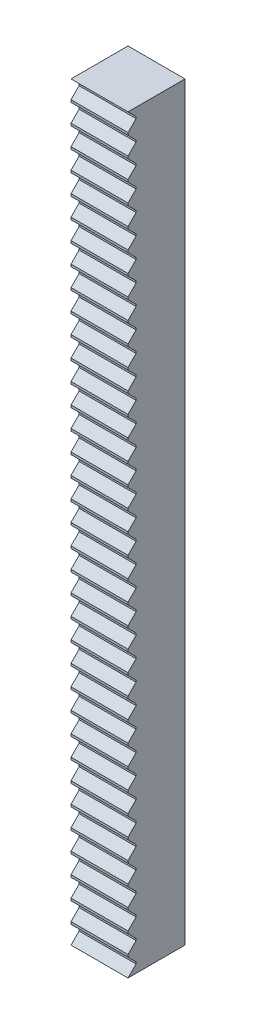
SolidWorks part; units mm, degrees
ref_plane "Front Plane" through (0, 0, 0) normal (0, 0, 1) x (1, 0, 0)
ref_plane "Top Plane" through (0, 0, 0) normal (0, 1, 0) x (1, 0, 0)
ref_plane "Right Plane" through (0, 0, 0) normal (1, 0, 0) x (0, 0, -1)
sketch "Sketch1" plane through (0, 0, 0) normal (0, 0, 1) x (1, 0, 0)
  line L1 (-9.5, 125) -> (9.5, 125)
  line L2 (-9.5, 125) -> (-9.5, -125)
  line L3 (-9.5, -125) -> (9.5, -125)
  line L4 (9.5, 125) -> (9.5, -125)
  line L5 (-9.5, 125) -> (9.5, -125) construction
  line L6 (-9.5, -125) -> (9.5, 125) construction
  point P0 (0, 0)
  dimension "D1" = 19
  dimension "D2" = 250
extrude "Boss-Extrude1" add sketch "Sketch1" along normal mid plane 19
sketch "Sketch2" plane through (-9.5, 0, 0) normal (-1, 0, 0) x (0, 0, 1)
  line L0 (9.5, 125) -> (6.8, 122.3)
  line L1 (6.8, 121.7) -> (9.5, 119)
  line L3 (9.5, 125) -> (9.5, -125) construction
  line L6 (9.5, 125) -> (10.5, 125)
  line L7 (10.5, 125) -> (10.5, 119)
  line L8 (10.5, 119) -> (9.5, 119)
  line L9 (6.8, 122.3) -> (6.8, 121.7)
  line L10 (9.5, 118.2222) -> (6.8, 115.5222)
  line L11 (6.8, 114.9222) -> (9.5, 112.2222)
  line L12 (9.5, 118.2222) -> (10.5, 118.2222)
  line L13 (10.5, 118.2222) -> (10.5, 112.2222)
  line L14 (10.5, 112.2222) -> (9.5, 112.2222)
  line L15 (6.8, 115.5222) -> (6.8, 114.9222)
  line L16 (9.5, 111.4444) -> (6.8, 108.7444)
  line L17 (6.8, 108.1444) -> (9.5, 105.4444)
  line L18 (9.5, 111.4444) -> (10.5, 111.4444)
  line L19 (10.5, 111.4444) -> (10.5, 105.4444)
  line L20 (10.5, 105.4444) -> (9.5, 105.4444)
  line L21 (6.8, 108.7444) -> (6.8, 108.1444)
  line L22 (9.5, 104.6667) -> (6.8, 101.9667)
  line L23 (6.8, 101.3667) -> (9.5, 98.6667)
  line L24 (9.5, 104.6667) -> (10.5, 104.6667)
  line L25 (10.5, 104.6667) -> (10.5, 98.6667)
  line L26 (10.5, 98.6667) -> (9.5, 98.6667)
  line L27 (6.8, 101.9667) -> (6.8, 101.3667)
  line L28 (9.5, 97.8889) -> (6.8, 95.1889)
  line L29 (6.8, 94.5889) -> (9.5, 91.8889)
  line L30 (9.5, 97.8889) -> (10.5, 97.8889)
  line L31 (10.5, 97.8889) -> (10.5, 91.8889)
  line L32 (10.5, 91.8889) -> (9.5, 91.8889)
  line L33 (6.8, 95.1889) -> (6.8, 94.5889)
  line L34 (9.5, 91.1111) -> (6.8, 88.4111)
  line L35 (6.8, 87.8111) -> (9.5, 85.1111)
  line L36 (9.5, 91.1111) -> (10.5, 91.1111)
  line L37 (10.5, 91.1111) -> (10.5, 85.1111)
  line L38 (10.5, 85.1111) -> (9.5, 85.1111)
  line L39 (6.8, 88.4111) -> (6.8, 87.8111)
  line L40 (9.5, 84.3333) -> (6.8, 81.6333)
  line L41 (6.8, 81.0333) -> (9.5, 78.3333)
  line L42 (9.5, 84.3333) -> (10.5, 84.3333)
  line L43 (10.5, 84.3333) -> (10.5, 78.3333)
  line L44 (10.5, 78.3333) -> (9.5, 78.3333)
  line L45 (6.8, 81.6333) -> (6.8, 81.0333)
  line L46 (9.5, 77.5556) -> (6.8, 74.8556)
  line L47 (6.8, 74.2556) -> (9.5, 71.5556)
  line L48 (9.5, 77.5556) -> (10.5, 77.5556)
  line L49 (10.5, 77.5556) -> (10.5, 71.5556)
  line L50 (10.5, 71.5556) -> (9.5, 71.5556)
  line L51 (6.8, 74.8556) -> (6.8, 74.2556)
  line L52 (9.5, 70.7778) -> (6.8, 68.0778)
  line L53 (6.8, 67.4778) -> (9.5, 64.7778)
  line L54 (9.5, 70.7778) -> (10.5, 70.7778)
  line L55 (10.5, 70.7778) -> (10.5, 64.7778)
  line L56 (10.5, 64.7778) -> (9.5, 64.7778)
  line L57 (6.8, 68.0778) -> (6.8, 67.4778)
  line L58 (9.5, 64) -> (6.8, 61.3)
  line L59 (6.8, 60.7) -> (9.5, 58)
  line L60 (9.5, 64) -> (10.5, 64)
  line L61 (10.5, 64) -> (10.5, 58)
  line L62 (10.5, 58) -> (9.5, 58)
  line L63 (6.8, 61.3) -> (6.8, 60.7)
  line L64 (9.5, 57.2222) -> (6.8, 54.5222)
  line L65 (6.8, 53.9222) -> (9.5, 51.2222)
  line L66 (9.5, 57.2222) -> (10.5, 57.2222)
  line L67 (10.5, 57.2222) -> (10.5, 51.2222)
  line L68 (10.5, 51.2222) -> (9.5, 51.2222)
  line L69 (6.8, 54.5222) -> (6.8, 53.9222)
  line L70 (9.5, 50.4444) -> (6.8, 47.7444)
  line L71 (6.8, 47.1444) -> (9.5, 44.4444)
  line L72 (9.5, 50.4444) -> (10.5, 50.4444)
  line L73 (10.5, 50.4444) -> (10.5, 44.4444)
  line L74 (10.5, 44.4444) -> (9.5, 44.4444)
  line L75 (6.8, 47.7444) -> (6.8, 47.1444)
  line L76 (9.5, 43.6667) -> (6.8, 40.9667)
  line L77 (6.8, 40.3667) -> (9.5, 37.6667)
  line L78 (9.5, 43.6667) -> (10.5, 43.6667)
  line L79 (10.5, 43.6667) -> (10.5, 37.6667)
  line L80 (10.5, 37.6667) -> (9.5, 37.6667)
  line L81 (6.8, 40.9667) -> (6.8, 40.3667)
  line L82 (9.5, 36.8889) -> (6.8, 34.1889)
  line L83 (6.8, 33.5889) -> (9.5, 30.8889)
  line L84 (9.5, 36.8889) -> (10.5, 36.8889)
  line L85 (10.5, 36.8889) -> (10.5, 30.8889)
  line L86 (10.5, 30.8889) -> (9.5, 30.8889)
  line L87 (6.8, 34.1889) -> (6.8, 33.5889)
  line L88 (9.5, 30.1111) -> (6.8, 27.4111)
  line L89 (6.8, 26.8111) -> (9.5, 24.1111)
  line L90 (9.5, 30.1111) -> (10.5, 30.1111)
  line L91 (10.5, 30.1111) -> (10.5, 24.1111)
  line L92 (10.5, 24.1111) -> (9.5, 24.1111)
  line L93 (6.8, 27.4111) -> (6.8, 26.8111)
  line L94 (9.5, 23.3333) -> (6.8, 20.6333)
  line L95 (6.8, 20.0333) -> (9.5, 17.3333)
  line L96 (9.5, 23.3333) -> (10.5, 23.3333)
  line L97 (10.5, 23.3333) -> (10.5, 17.3333)
  line L98 (10.5, 17.3333) -> (9.5, 17.3333)
  line L99 (6.8, 20.6333) -> (6.8, 20.0333)
  line L100 (9.5, 16.5556) -> (6.8, 13.8556)
  line L101 (6.8, 13.2556) -> (9.5, 10.5556)
  line L102 (9.5, 16.5556) -> (10.5, 16.5556)
  line L103 (10.5, 16.5556) -> (10.5, 10.5556)
  line L104 (10.5, 10.5556) -> (9.5, 10.5556)
  line L105 (6.8, 13.8556) -> (6.8, 13.2556)
  line L106 (9.5, 9.7778) -> (6.8, 7.0778)
  line L107 (6.8, 6.4778) -> (9.5, 3.7778)
  line L108 (9.5, 9.7778) -> (10.5, 9.7778)
  line L109 (10.5, 9.7778) -> (10.5, 3.7778)
  line L110 (10.5, 3.7778) -> (9.5, 3.7778)
  line L111 (6.8, 7.0778) -> (6.8, 6.4778)
  line L112 (9.5, 3) -> (6.8, 0.3)
  line L113 (6.8, -0.3) -> (9.5, -3)
  line L114 (9.5, 3) -> (10.5, 3)
  line L115 (10.5, 3) -> (10.5, -3)
  line L116 (10.5, -3) -> (9.5, -3)
  line L117 (6.8, 0.3) -> (6.8, -0.3)
  line L118 (9.5, -3.7778) -> (6.8, -6.4778)
  line L119 (6.8, -7.0778) -> (9.5, -9.7778)
  line L120 (9.5, -3.7778) -> (10.5, -3.7778)
  line L121 (10.5, -3.7778) -> (10.5, -9.7778)
  line L122 (10.5, -9.7778) -> (9.5, -9.7778)
  line L123 (6.8, -6.4778) -> (6.8, -7.0778)
  line L124 (9.5, -10.5556) -> (6.8, -13.2556)
  line L125 (6.8, -13.8556) -> (9.5, -16.5556)
  line L126 (9.5, -10.5556) -> (10.5, -10.5556)
  line L127 (10.5, -10.5556) -> (10.5, -16.5556)
  line L128 (10.5, -16.5556) -> (9.5, -16.5556)
  line L129 (6.8, -13.2556) -> (6.8, -13.8556)
  line L130 (9.5, -17.3333) -> (6.8, -20.0333)
  line L131 (6.8, -20.6333) -> (9.5, -23.3333)
  line L132 (9.5, -17.3333) -> (10.5, -17.3333)
  line L133 (10.5, -17.3333) -> (10.5, -23.3333)
  line L134 (10.5, -23.3333) -> (9.5, -23.3333)
  line L135 (6.8, -20.0333) -> (6.8, -20.6333)
  line L136 (9.5, -24.1111) -> (6.8, -26.8111)
  line L137 (6.8, -27.4111) -> (9.5, -30.1111)
  line L138 (9.5, -24.1111) -> (10.5, -24.1111)
  line L139 (10.5, -24.1111) -> (10.5, -30.1111)
  line L140 (10.5, -30.1111) -> (9.5, -30.1111)
  line L141 (6.8, -26.8111) -> (6.8, -27.4111)
  line L142 (9.5, -30.8889) -> (6.8, -33.5889)
  line L143 (6.8, -34.1889) -> (9.5, -36.8889)
  line L144 (9.5, -30.8889) -> (10.5, -30.8889)
  line L145 (10.5, -30.8889) -> (10.5, -36.8889)
  line L146 (10.5, -36.8889) -> (9.5, -36.8889)
  line L147 (6.8, -33.5889) -> (6.8, -34.1889)
  line L148 (9.5, -37.6667) -> (6.8, -40.3667)
  line L149 (6.8, -40.9667) -> (9.5, -43.6667)
  line L150 (9.5, -37.6667) -> (10.5, -37.6667)
  line L151 (10.5, -37.6667) -> (10.5, -43.6667)
  line L152 (10.5, -43.6667) -> (9.5, -43.6667)
  line L153 (6.8, -40.3667) -> (6.8, -40.9667)
  line L154 (9.5, -44.4444) -> (6.8, -47.1444)
  line L155 (6.8, -47.7444) -> (9.5, -50.4444)
  line L156 (9.5, -44.4444) -> (10.5, -44.4444)
  line L157 (10.5, -44.4444) -> (10.5, -50.4444)
  line L158 (10.5, -50.4444) -> (9.5, -50.4444)
  line L159 (6.8, -47.1444) -> (6.8, -47.7444)
  line L160 (9.5, -51.2222) -> (6.8, -53.9222)
  line L161 (6.8, -54.5222) -> (9.5, -57.2222)
  line L162 (9.5, -51.2222) -> (10.5, -51.2222)
  line L163 (10.5, -51.2222) -> (10.5, -57.2222)
  line L164 (10.5, -57.2222) -> (9.5, -57.2222)
  line L165 (6.8, -53.9222) -> (6.8, -54.5222)
  line L166 (9.5, -58) -> (6.8, -60.7)
  line L167 (6.8, -61.3) -> (9.5, -64)
  line L168 (9.5, -58) -> (10.5, -58)
  line L169 (10.5, -58) -> (10.5, -64)
  line L170 (10.5, -64) -> (9.5, -64)
  line L171 (6.8, -60.7) -> (6.8, -61.3)
  line L172 (9.5, -64.7778) -> (6.8, -67.4778)
  line L173 (6.8, -68.0778) -> (9.5, -70.7778)
  line L174 (9.5, -64.7778) -> (10.5, -64.7778)
  line L175 (10.5, -64.7778) -> (10.5, -70.7778)
  line L176 (10.5, -70.7778) -> (9.5, -70.7778)
  line L177 (6.8, -67.4778) -> (6.8, -68.0778)
  line L178 (9.5, -71.5556) -> (6.8, -74.2556)
  line L179 (6.8, -74.8556) -> (9.5, -77.5556)
  line L180 (9.5, -71.5556) -> (10.5, -71.5556)
  line L181 (10.5, -71.5556) -> (10.5, -77.5556)
  line L182 (10.5, -77.5556) -> (9.5, -77.5556)
  line L183 (6.8, -74.2556) -> (6.8, -74.8556)
  line L184 (9.5, -78.3333) -> (6.8, -81.0333)
  line L185 (6.8, -81.6333) -> (9.5, -84.3333)
  line L186 (9.5, -78.3333) -> (10.5, -78.3333)
  line L187 (10.5, -78.3333) -> (10.5, -84.3333)
  line L188 (10.5, -84.3333) -> (9.5, -84.3333)
  line L189 (6.8, -81.0333) -> (6.8, -81.6333)
  line L190 (9.5, -85.1111) -> (6.8, -87.8111)
  line L191 (6.8, -88.4111) -> (9.5, -91.1111)
  line L192 (9.5, -85.1111) -> (10.5, -85.1111)
  line L193 (10.5, -85.1111) -> (10.5, -91.1111)
  line L194 (10.5, -91.1111) -> (9.5, -91.1111)
  line L195 (6.8, -87.8111) -> (6.8, -88.4111)
  line L196 (9.5, -91.8889) -> (6.8, -94.5889)
  line L197 (6.8, -95.1889) -> (9.5, -97.8889)
  line L198 (9.5, -91.8889) -> (10.5, -91.8889)
  line L199 (10.5, -91.8889) -> (10.5, -97.8889)
  line L200 (10.5, -97.8889) -> (9.5, -97.8889)
  line L201 (6.8, -94.5889) -> (6.8, -95.1889)
  line L202 (9.5, -98.6667) -> (6.8, -101.3667)
  line L203 (6.8, -101.9667) -> (9.5, -104.6667)
  line L204 (9.5, -98.6667) -> (10.5, -98.6667)
  line L205 (10.5, -98.6667) -> (10.5, -104.6667)
  line L206 (10.5, -104.6667) -> (9.5, -104.6667)
  line L207 (6.8, -101.3667) -> (6.8, -101.9667)
  line L208 (9.5, -105.4444) -> (6.8, -108.1444)
  line L209 (6.8, -108.7444) -> (9.5, -111.4444)
  line L210 (9.5, -105.4444) -> (10.5, -105.4444)
  line L211 (10.5, -105.4444) -> (10.5, -111.4444)
  line L212 (10.5, -111.4444) -> (9.5, -111.4444)
  line L213 (6.8, -108.1444) -> (6.8, -108.7444)
  line L214 (9.5, -112.2222) -> (6.8, -114.9222)
  line L215 (6.8, -115.5222) -> (9.5, -118.2222)
  line L216 (9.5, -112.2222) -> (10.5, -112.2222)
  line L217 (10.5, -112.2222) -> (10.5, -118.2222)
  line L218 (10.5, -118.2222) -> (9.5, -118.2222)
  line L219 (6.8, -114.9222) -> (6.8, -115.5222)
  line L220 (9.5, -119) -> (6.8, -121.7)
  line L221 (6.8, -122.3) -> (9.5, -125)
  line L222 (9.5, -119) -> (10.5, -119)
  line L223 (10.5, -119) -> (10.5, -125)
  line L224 (10.5, -125) -> (9.5, -125)
  line L225 (6.8, -121.7) -> (6.8, -122.3)
  dimension "D1" = 6
  dimension "D2" = 2.7
  dimension "D3" = 2.7
  dimension "D4" = 1
extrude "Cut-Extrude1" cut sketch "Sketch2" against normal blind 29
